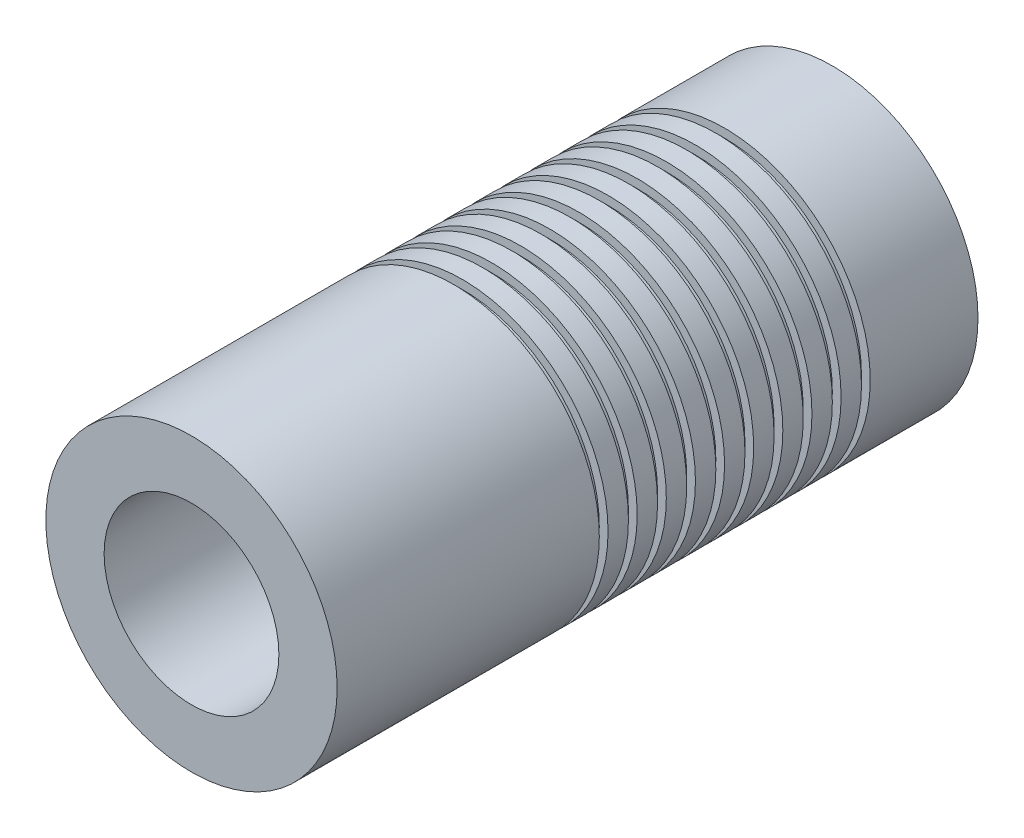
SolidWorks part; units mm, degrees
ref_plane "Front Plane" through (0, 0, 0) normal (0, 0, 1) x (1, 0, 0)
ref_plane "Top Plane" through (0, 0, 0) normal (0, 1, 0) x (1, 0, 0)
ref_plane "Right Plane" through (0, 0, 0) normal (1, 0, 0) x (0, 0, -1)
sketch "Sketch1" plane through (0, 0, 0) normal (0, 0, 1) x (1, 0, 0)
  circle A0 centre (0, 0) radius 5
  dimension "D1" = 10
extrude "Boss-Extrude1" add sketch "Sketch1" against normal blind 13 and the other way blind 9
sketch "Sketch2" plane through (0, 0, 9) normal (0, 0, 1) x (1, 0, 0)
  circle A0 centre (0, 0) radius 3
  dimension "D1" = 6
extrude "Cut-Extrude1" cut sketch "Sketch2" against normal blind 5
sketch "Sketch3" plane through (0, 0, -13) normal (0, 0, -1) x (-1, 0, 0)
  circle A0 centre (0, 0) radius 4
  dimension "D1" = 8
extrude "Cut-Extrude2" cut sketch "Sketch3" against normal blind 5
sketch "Sketch5" plane through (0, 0, 0) normal (0, 0, 1) x (1, 0, 0)
  circle A0 centre (0, 0) radius 5
  circle A1 centre (0, 0) radius 4.7
  dimension "D1" = 10
  dimension "D2" = 0.3
extrude "Cut-Extrude3" cut sketch "Sketch5" against normal blind 0.3
sketch "Sketch6" plane through (0, 0, 0) normal (0, 1, 0) x (1, 0, 0)
  line L0 (0, 0) -> (0, 8.5599) construction
pattern_linear "LPattern1" count 10 spacing 1 along (0, 0, -1) of "Cut-Extrude3"
